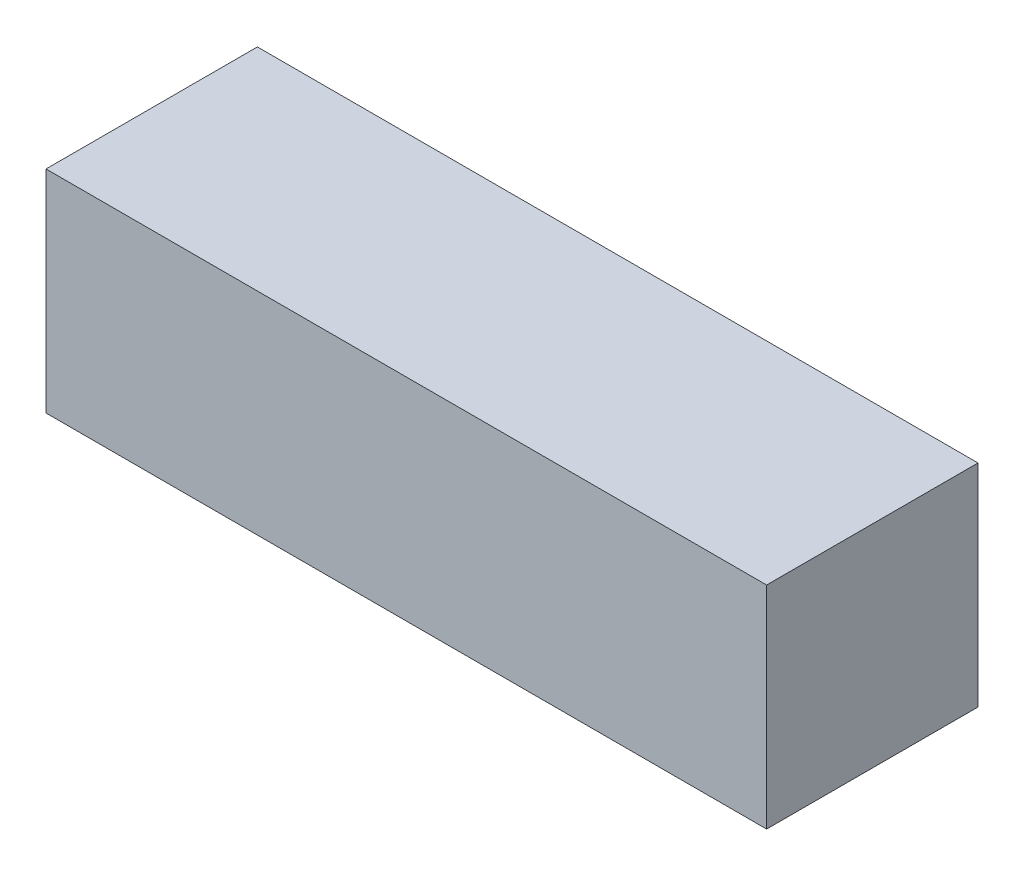
SolidWorks part; units mm, degrees
ref_plane "Front Plane" through (0, 0, 0) normal (0, 0, 1) x (1, 0, 0)
ref_plane "Top Plane" through (0, 0, 0) normal (0, 1, 0) x (1, 0, 0)
ref_plane "Right Plane" through (0, 0, 0) normal (1, 0, 0) x (0, 0, -1)
sketch "Sketch1" plane through (0, 0, 0) normal (0, 1, 0) x (1, 0, 0)
  line L1 (0, 0) -> (38.1, 0)
  line L2 (0, 0) -> (0, 11.176)
  line L3 (0, 11.176) -> (38.1, 11.176)
  line L4 (38.1, 0) -> (38.1, 11.176)
  dimension "D1" = 11.176
  dimension "D2" = 38.1
extrude "Boss-Extrude1" add sketch "Sketch1" along normal blind 11.176
shell "Shell1" thickness 2.286
